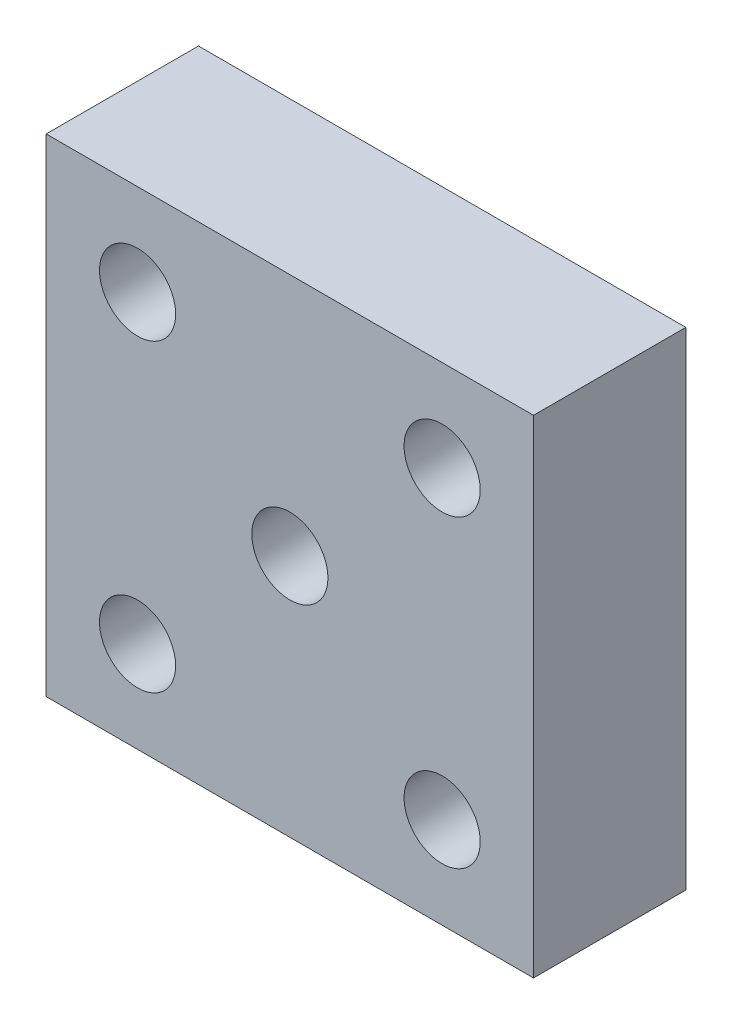
SolidWorks part; units mm, degrees
ref_plane "Front Plane" through (0, 0, 0) normal (0, 0, 1) x (1, 0, 0)
ref_plane "Top Plane" through (0, 0, 0) normal (0, 1, 0) x (1, 0, 0)
ref_plane "Right Plane" through (0, 0, 0) normal (1, 0, 0) x (0, 0, -1)
sketch "Sketch1" plane through (0, 0, 0) normal (0, 0, 1) x (1, 0, 0)
  line L1 (-8, 8) -> (8, 8)
  line L2 (-8, 8) -> (-8, -8)
  line L3 (-8, -8) -> (8, -8)
  line L4 (8, 8) -> (8, -8)
  circle A0 centre (-5, 5) radius 1.25
  circle A1 centre (5, 5) radius 1.25
  circle A2 centre (5, -5) radius 1.25
  circle A3 centre (-5, -5) radius 1.25
  circle A4 centre (0, 0) radius 1.25
  point P15 (0, 0)
  point P16 (0, 8)
  point P17 (-8, 0)
  point P18 (0, 0)
  point P19 (20, -19.6852)
  point P20 (0, 0)
  dimension "D1" = 2.5
  dimension "D2" = 10
  dimension "D3" = 10
  dimension "D4" = 3
  dimension "D5" = 3
  dimension "D6" = 3
  dimension "D7" = 3
extrude "Boss-Extrude1" add sketch "Sketch1" along normal blind 5
